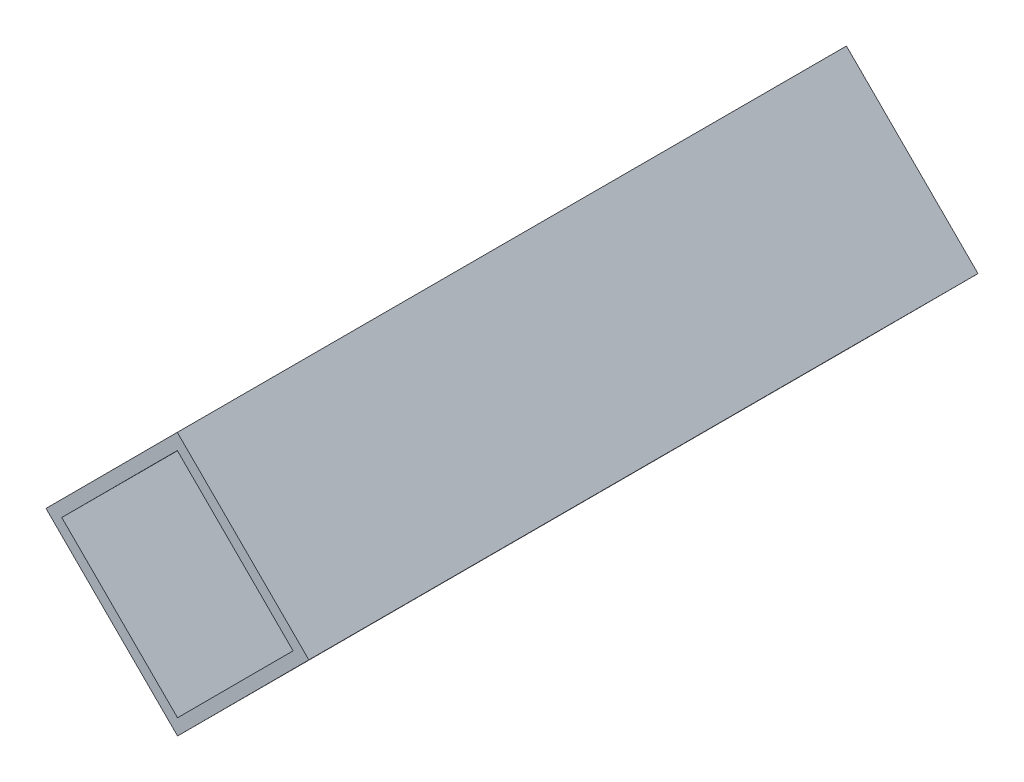
SolidWorks part; units mm, degrees
material "可鍛鑄鐵"
ref_plane "前基準面" through (0, 0, 0) normal (0, 0, 1) x (1, 0, 0)
ref_plane "上基準面" through (0, 0, 0) normal (0, 1, 0) x (1, 0, 0)
ref_plane "右基準面" through (0, 0, 0) normal (1, 0, 0) x (0, 0, -1)
sketch "草圖1" plane through (0, 0, 0) normal (0, 0, 1) x (1, 0, 0)
  line L0 (0, 0) -> (17.6938, -17.6615)
  line L1 (0, 0) -> (-17.6615, -17.6938)
  line L2 (17.6938, -17.6615) -> (0.0323, -35.3553)
  line L3 (-17.6615, -17.6938) -> (0.0323, -35.3553)
  line L4 (0.0019, -2.1213) -> (-15.5402, -17.6919)
  line L5 (0.0019, -2.1213) -> (15.5725, -17.6635)
  line L6 (-15.5402, -17.6919) -> (0.0303, -33.234)
  line L7 (15.5725, -17.6635) -> (0.0303, -33.234)
  point P0 (8.8469, -8.8308)
  dimension "D1" = 25
  dimension "D2" = 25
  dimension "D3" = 1.5
  dimension "D4" = 1.5
  dimension "D5" = 1.5
  dimension "D6" = 1.5
extrude "填料-伸長1" add sketch "草圖1" along normal blind 90
sketch "草圖2" plane through (0, 0, 0) normal (0.7065, 0.7078, 0) x (0.7078, -0.7065, 0)
  line L0 (25, -90) -> (0, -90) construction
  line L1 (25, -90) -> (25, 0) construction
  line L2 (25, 0) -> (0, 0) construction
  line L3 (0, -90) -> (0, 0) construction
  circle A0 centre (12.5, 82) radius 2.75
  circle A1 centre (12.5, 38) radius 2.75
  circle A2 centre (12.5, -128) radius 2.75
  circle A3 centre (12.5, -172) radius 2.75
  dimension "D1" = 5.5
  dimension "D2" = 5.5
  dimension "D4" = 128
  dimension "D5" = 12.5
  dimension "D6" = 12.5
  dimension "D7" = 5.5
  dimension "D8" = 5.5
  dimension "D9" = 44
  dimension "D10" = 128
  dimension "D11" = 12.5
  dimension "D3" = 44
